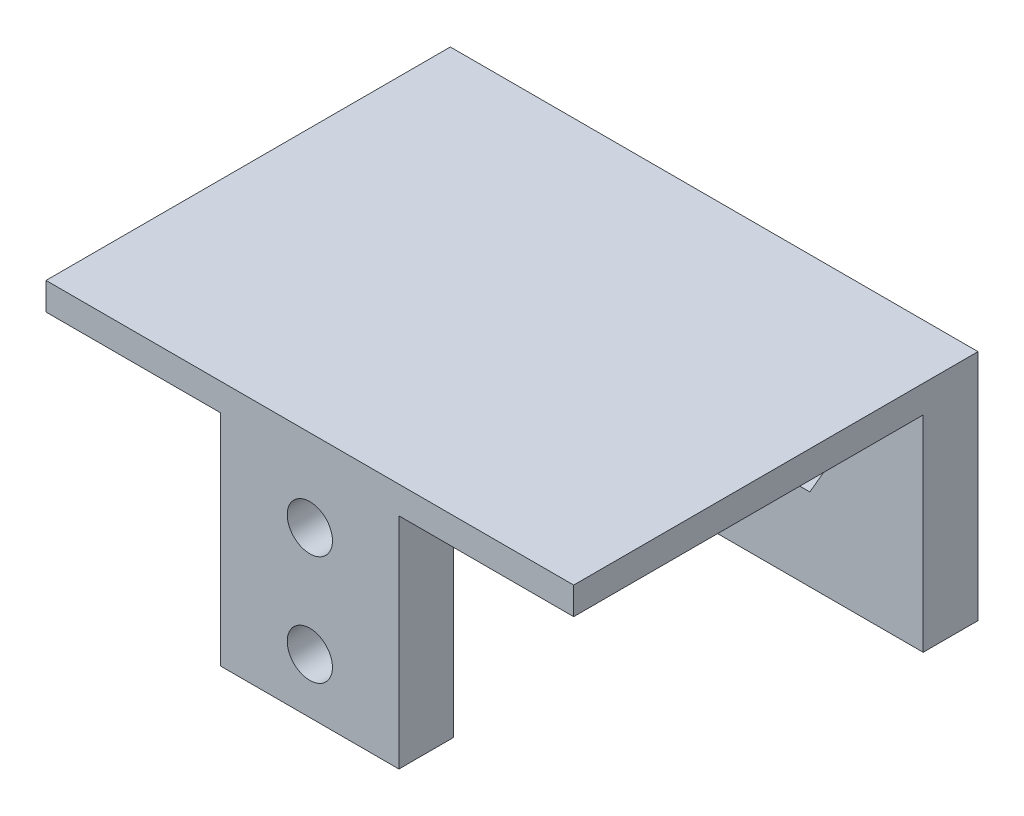
SolidWorks part; units mm, degrees
ref_plane "Front Plane" through (0, 0, 0) normal (0, 0, 1) x (1, 0, 0)
ref_plane "Top Plane" through (0, 0, 0) normal (0, 1, 0) x (1, 0, 0)
ref_plane "Right Plane" through (0, 0, 0) normal (1, 0, 0) x (0, 0, -1)
sketch "Sketch1" plane through (0, 0, 0) normal (0, 1, 0) x (1, 0, 0)
  line L1 (0, 0) -> (38.5, 0)
  line L2 (0, 0) -> (0, -29.5)
  line L3 (0, -29.5) -> (38.5, -29.5)
  line L4 (38.5, 0) -> (38.5, -29.5)
  dimension "D1" = 29.5
  dimension "D2" = 38.5
extrude "Boss-Extrude1" add sketch "Sketch1" along normal blind 2
sketch "Sketch2" plane through (0, 0, 29.5) normal (0, 0, 1) x (1, 0, 0)
  line L0 (0, 0) -> (38.5, 0) construction
  line L1 (12.75, 0) -> (25.75, 0)
  line L2 (12.75, 0) -> (12.75, -16)
  line L3 (12.75, -16) -> (25.75, -16)
  line L4 (25.75, 0) -> (25.75, -16)
  line L5 (0, 2) -> (0, 0) construction
  dimension "D1" = 12.75
  dimension "D2" = 13
  dimension "D3" = 16
extrude "Boss-Extrude2" add sketch "Sketch2" against normal blind 4
sketch "Sketch3" plane through (0, 0, 0) normal (0, -1, 0) x (1, 0, 0)
  line L0 (0, 0) -> (0, 29.5) construction
  line L1 (38.5, 0) -> (0, 0)
  line L2 (38.5, 0) -> (38.5, 4)
  line L3 (38.5, 4) -> (0, 4)
  line L4 (0, 0) -> (0, 4)
  dimension "D1" = 4
extrude "Boss-Extrude3" add sketch "Sketch3" along normal blind 15
sketch "Sketch4" plane through (0, 0, 29.5) normal (0, 0, 1) x (1, 0, 0)
  line L0 (12.75, 0) -> (12.75, -16) construction
  line L1 (25.75, -16) -> (25.75, 0) construction
  line L2 (12.75, -16) -> (25.75, -16) construction
  circle A0 centre (19.25, -4) radius 1.65
  circle A1 centre (19.25, -12) radius 1.65
  dimension "D5" = 3.3
  dimension "D6" = 3.3
  dimension "D1" = 6.5
  dimension "D2" = 6.5
  dimension "D3" = 4
  dimension "D4" = 8
extrude "Cut-Extrude1" cut sketch "Sketch4" against normal blind 15
sketch "Sketch5" plane through (0, 0, 4) normal (0, 0, 1) x (1, 0, 0)
  line L0 (0, -15) -> (0, 0) construction
  line L1 (11.7321, -9) -> (13.4641, -6)
  line L2 (13.4641, -6) -> (11.7321, -3)
  line L3 (11.7321, -3) -> (8.2679, -3)
  line L4 (8.2679, -3) -> (6.5359, -6)
  line L5 (6.5359, -6) -> (8.2679, -9)
  line L6 (8.2679, -9) -> (11.7321, -9)
  line L7 (30.2321, -9) -> (31.9641, -6)
  line L8 (31.9641, -6) -> (30.2321, -3)
  line L9 (30.2321, -3) -> (26.7679, -3)
  line L10 (26.7679, -3) -> (25.0359, -6)
  line L11 (25.0359, -6) -> (26.7679, -9)
  line L12 (26.7679, -9) -> (30.2321, -9)
  line L13 (38.5, 0) -> (0, 0) construction
  line L14 (38.5, -15) -> (38.5, 0) construction
  circle A0 centre (10, -6) radius 3 construction
  circle A1 centre (28.5, -6) radius 3 construction
  dimension "D1" = 6
  dimension "D6" = 6
  dimension "D2" = 10
  dimension "D3" = 6
  dimension "D4" = 6
  dimension "D5" = 10
  dimension "D7" = 3
  dimension "D8" = 3
extrude "Cut-Extrude2" cut sketch "Sketch5" against normal blind 2.5
sketch "Sketch6" plane through (0, 0, 1.5) normal (0, 0, 1) x (1, 0, 0)
  line L0 (11.7321, -3) -> (8.2679, -3) construction
  line L1 (8.2679, -3) -> (6.5359, -6) construction
  line L2 (30.2321, -3) -> (26.7679, -3) construction
  line L3 (26.7679, -3) -> (25.0359, -6) construction
  circle A0 centre (10, -6) radius 1.65
  circle A1 centre (28.5, -6) radius 1.65
  dimension "D3" = 3.3
  dimension "D6" = 3.3
  dimension "D1" = 3
  dimension "D2" = 3
  dimension "D4" = 3
  dimension "D5" = 3
extrude "Cut-Extrude3" cut sketch "Sketch6" against normal blind 2.5
